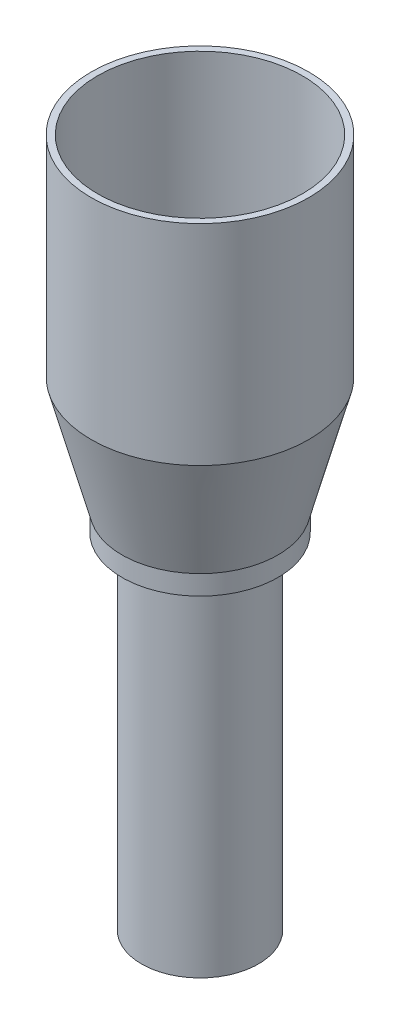
SolidWorks part; units mm, degrees
ref_plane "Plan de face" through (0, 0, 0) normal (0, 0, 1) x (1, 0, 0)
ref_plane "Plan de dessus" through (0, 0, 0) normal (0, 1, 0) x (1, 0, 0)
ref_plane "Plan de droite" through (0, 0, 0) normal (1, 0, 0) x (0, 0, -1)
sketch "Esquisse2" plane through (0, 0, 0) normal (0, 0, 1) x (1, 0, 0)
  line L0 (-28.9326, 21.279) -> (37.2063, 21.279) construction
  line L1 (9, 49.3634) -> (9, -31.721) construction
  line L2 (0, 49.3634) -> (0, -31.721) construction
  line L3 (-28.9326, 24.279) -> (37.2063, 24.279) construction
  line L4 (12, 49.3634) -> (12, -31.721) construction
  line L5 (-28.9326, -31.721) -> (37.2063, -31.721) construction
  line L6 (9, -31.721) -> (8, -31.721)
  line L7 (8, -31.721) -> (8, -31.6409)
  line L8 (9, -31.721) -> (9, 21.279)
  line L9 (9, 21.279) -> (12, 21.279)
  line L10 (12, 21.279) -> (12, 24.279)
  line L11 (-13.3791, 74.279) -> (33.6717, 74.279) construction
  line L12 (16.75, 66.4662) -> (16.75, 7.2906) construction
  line L13 (-19.5507, 44.279) -> (33.6717, 44.279) construction
  line L14 (12, 24.279) -> (16.75, 42.036)
  line L15 (16.75, 42.036) -> (16.75, 74.279)
  line L17 (8, -31.6409) -> (8, 22.279)
  line L18 (8, 22.279) -> (15.75, 42.1674)
  line L21 (15.75, 42.1674) -> (15.75, 74.279)
  line L22 (15.75, 74.279) -> (16.75, 74.279)
  line L23 (7.4, -41.6463) -> (9, -31.721) construction
  line L25 (8, 22.279) -> (11, 22.279) construction
  line L26 (11, 22.279) -> (11, 24.4104) construction
  line L27 (11, 24.4104) -> (15.75, 42.1674) construction
  line L28 (6.4127, -41.4872) -> (8, -31.6409) construction
  dimension "D1" = 9
  dimension "D2" = 53
  dimension "D3" = 3
  dimension "D4" = 3
  dimension "D6" = 50
  dimension "D7" = 16.75
  dimension "D8" = 20
  dimension "D9" = 1
revolve "Révolution1" add sketch "Esquisse2" angle 360 about L2
